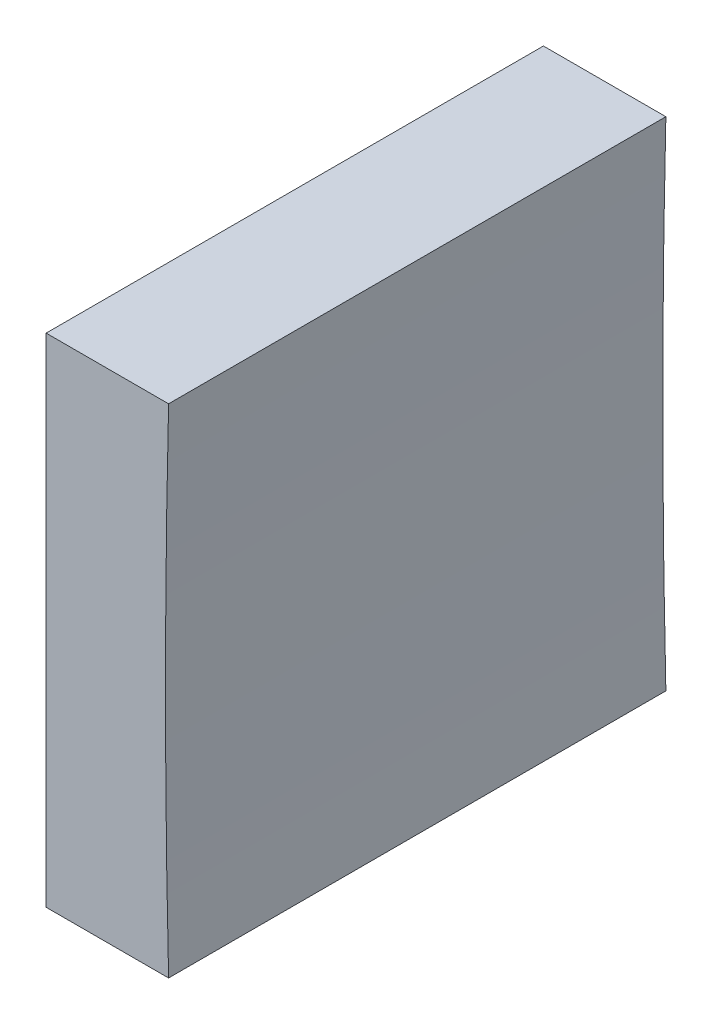
SolidWorks part; units mm, degrees
ref_plane "前视基准面" through (0, 0, 0) normal (0, 0, 1) x (1, 0, 0)
ref_plane "上视基准面" through (0, 0, 0) normal (0, 1, 0) x (1, 0, 0)
ref_plane "右视基准面" through (0, 0, 0) normal (1, 0, 0) x (0, 0, -1)
sketch "草图1" plane through (0, 0, 0) normal (0, 0, 1) x (1, 0, 0)
  line L0 (278.655, 66.8579) -> (298.183, 66.8579) construction
  line L1 (284.7071, 66.8579) -> (284.7071, 79.3579)
  line L2 (284.7071, 79.3579) -> (290.8634, 79.3579)
  line L3 (290.8634, 54.3579) -> (284.7071, 54.3579)
  line L4 (284.7071, 54.3579) -> (284.7071, 66.8579)
  arc A0 (290.8634, 79.3579) -> (290.8634, 54.3579) centre (790.7071, 66.8579) ccw
  dimension "D1" = 500
  dimension "D2" = 6.1563
extrude "凸台-拉伸1" add sketch "草图1" along normal blind 25
